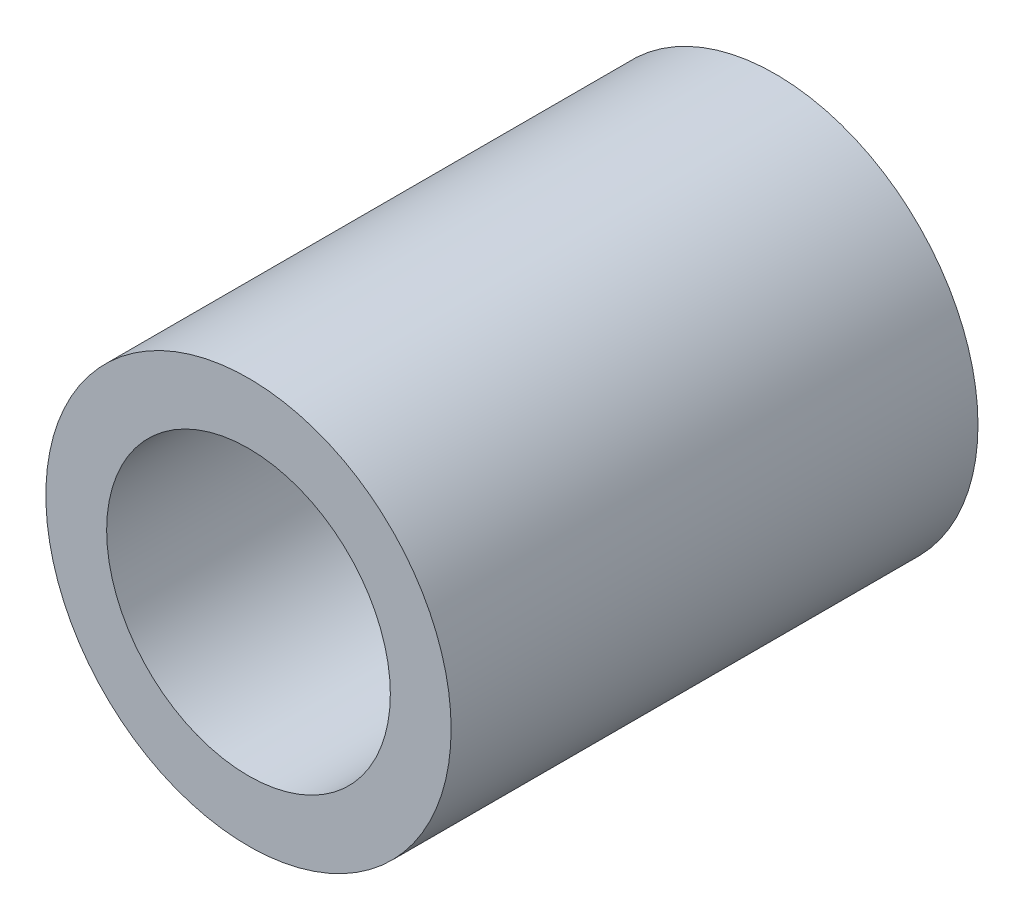
SolidWorks part; units mm, degrees
ref_plane "Plano frontal" through (0, 0, 0) normal (0, 0, 1) x (1, 0, 0)
ref_plane "Plano superior" through (0, 0, 0) normal (0, 1, 0) x (1, 0, 0)
ref_plane "Plano direito" through (0, 0, 0) normal (1, 0, 0) x (0, 0, -1)
sketch "Esboço1" plane through (0, 0, 0) normal (0, 0, 1) x (1, 0, 0)
  circle A0 centre (0, 0) radius 1.75
  circle A1 centre (0, 0) radius 2.5
  dimension "D1" = 3.5
  dimension "D2" = 5
extrude "Ressalto-extrusão1" add sketch "Esboço1" along normal blind 6.5
